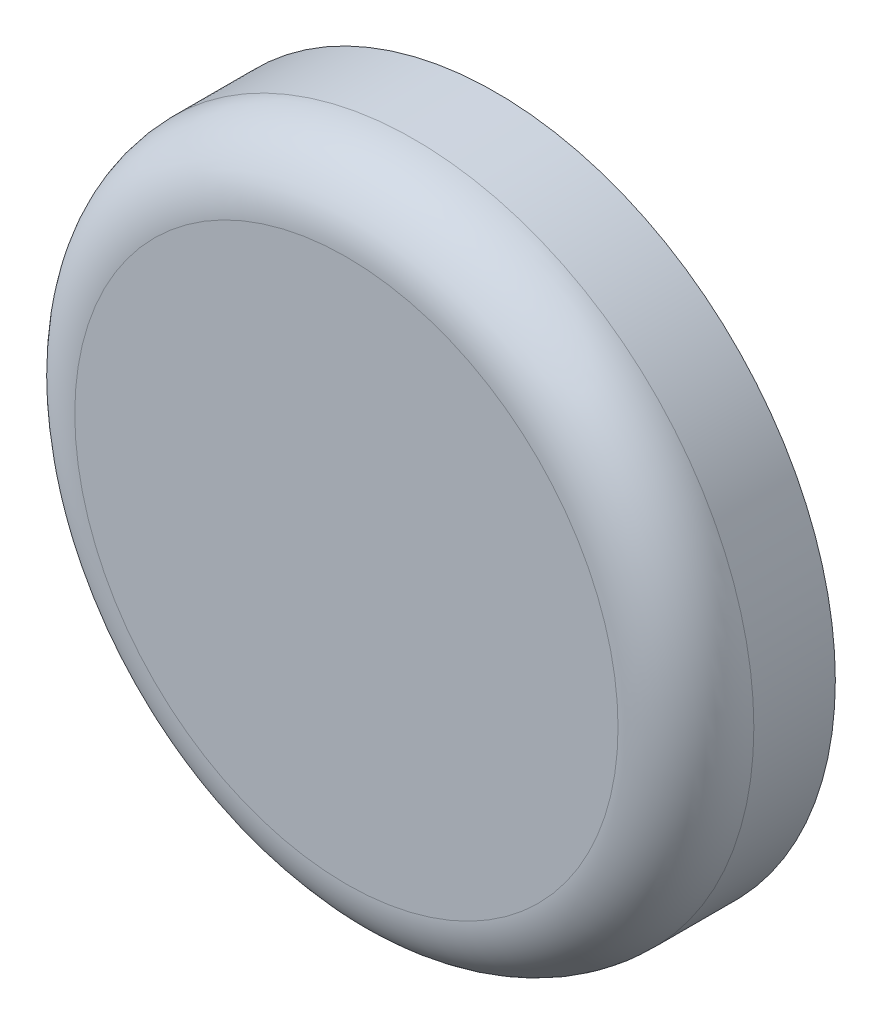
SolidWorks part; units mm, degrees
ref_plane "Alzado" through (0, 0, 0) normal (0, 0, 1) x (1, 0, 0)
ref_plane "Planta" through (0, 0, 0) normal (0, 1, 0) x (1, 0, 0)
ref_plane "Vista lateral" through (0, 0, 0) normal (1, 0, 0) x (0, 0, -1)
sketch "Croquis1" plane through (0, 0, 0) normal (0, 0, 1) x (1, 0, 0)
  line L0 (0.625, 7.5) -> (-11.875, 20) construction
  line L1 (-11.875, 20) -> (-11.875, 7.5) construction
  line L2 (-11.875, 7.5) -> (0.625, 20) construction
  circle A0 centre (-5.625, 13.75) radius 25
  dimension "D1" = 50
extrude "Saliente-Extruir1" add sketch "Croquis1" along normal blind 11
fillet "Redondeo1" radius 5 1 edges at (19.375, 13.75, 11)
sketch "Croquis2" plane through (0, 0, 0) normal (0, 0, -1) x (-1, 0, 0)
  circle A0 centre (5.625, 13.75) radius 5.875
  dimension "D1" = 11.75
extrude "Cortar-Extruir1" cut sketch "Croquis2" against normal blind 9
sketch "Croquis3" plane through (0, 0, 0) normal (0, 0, -1) x (-1, 0, 0)
  circle A0 centre (5.625, 13.75) radius 7
  dimension "D1" = 14
extrude "Cortar-Extruir2" cut sketch "Croquis3" against normal blind 4.5
